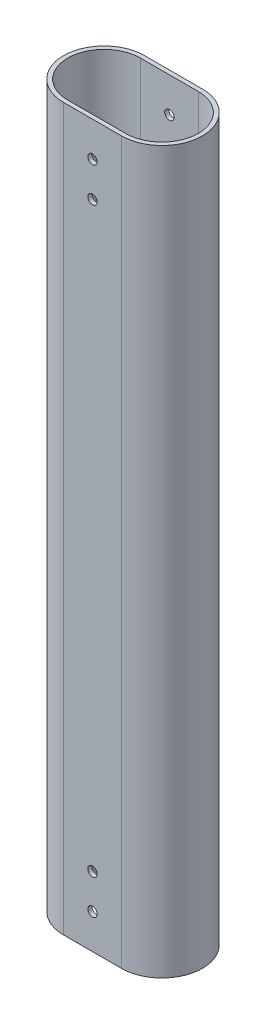
SolidWorks part; units mm, degrees
ref_plane "前基準面" through (0, 0, 0) normal (0, 0, 1) x (1, 0, 0)
ref_plane "上基準面" through (0, 0, 0) normal (0, 1, 0) x (1, 0, 0)
ref_plane "右基準面" through (0, 0, 0) normal (1, 0, 0) x (0, 0, -1)
sketch "草圖1" plane through (0, 0, 0) normal (0, 1, 0) x (1, 0, 0)
  line L0 (-12.5, 15.7) -> (12.5, 15.7)
  line L1 (-12.5, 17.5) -> (12.5, 17.5)
  line L2 (-12.5, -15.7) -> (12.5, -15.7)
  line L3 (-12.5, -17.5) -> (12.5, -17.5)
  line L5 (-12.5, 17.5) -> (12.5, -17.5) construction
  line L6 (-12.5, -17.5) -> (12.5, 17.5) construction
  arc A0 (12.5, -17.5) -> (12.5, 17.5) centre (12.5, 0) ccw
  arc A1 (-12.5, 17.5) -> (-12.5, -17.5) centre (-12.5, 0) ccw
  arc A2 (12.5, -15.7) -> (12.5, 15.7) centre (12.5, 0) ccw
  arc A3 (-12.5, 15.7) -> (-12.5, -15.7) centre (-12.5, 0) ccw
  point P0 (0, 0)
  dimension "D1" = 25
  dimension "D2" = 35
  dimension "D3" = 1.8
extrude "填料-伸長1" add sketch "草圖1" along normal blind 311.4
hole_wizard "#10-32 螺紋孔1" positions "草圖4" profile "草圖3" tap size "#10-32" standard "Ansi 英吋" end condition through all
sketch "草圖4" plane through (0, 0, 17.5) normal (0, 0, 1) x (1, 0, 0)
  line L0 (0, 0) -> (0, 311.4) construction
  line L2 (-12.5, 311.4) -> (12.5, 311.4) construction
  line L3 (-12.5, 0) -> (12.5, 0) construction
  point P0 (0, 15)
  point P8 (0, 30)
  point P19 (0, 296.4)
  point P21 (0, 281.4)
  dimension "D1" = 15
  dimension "D2" = 30
  dimension "D3" = 15
  dimension "D4" = 30
sketch "草圖3" plane through (0, 15, 17.5) normal (1, 0, 0) x (0, -1, 0)
  line L0 (0, 0) -> (0, 35)
  line L1 (0, 35) -> (2.0193, 35)
  line L2 (2.0193, 35) -> (2.0193, 0)
  line L5 (2.0193, 0) -> (0, 0)
  line L11 (0, -6.35) -> (0, 107.95) construction
  dimension "貫穿螺孔鑽直徑" = 4.0386
  dimension "貫穿螺孔鑽深度" = 35
cosmetic thread "鑽孔螺紋1" parameters "D2"=4.826
cosmetic thread "鑽孔螺紋2" parameters "D2"=4.826
cosmetic thread "鑽孔螺紋3" parameters "D2"=4.826
cosmetic thread "鑽孔螺紋4" parameters "D2"=4.826
